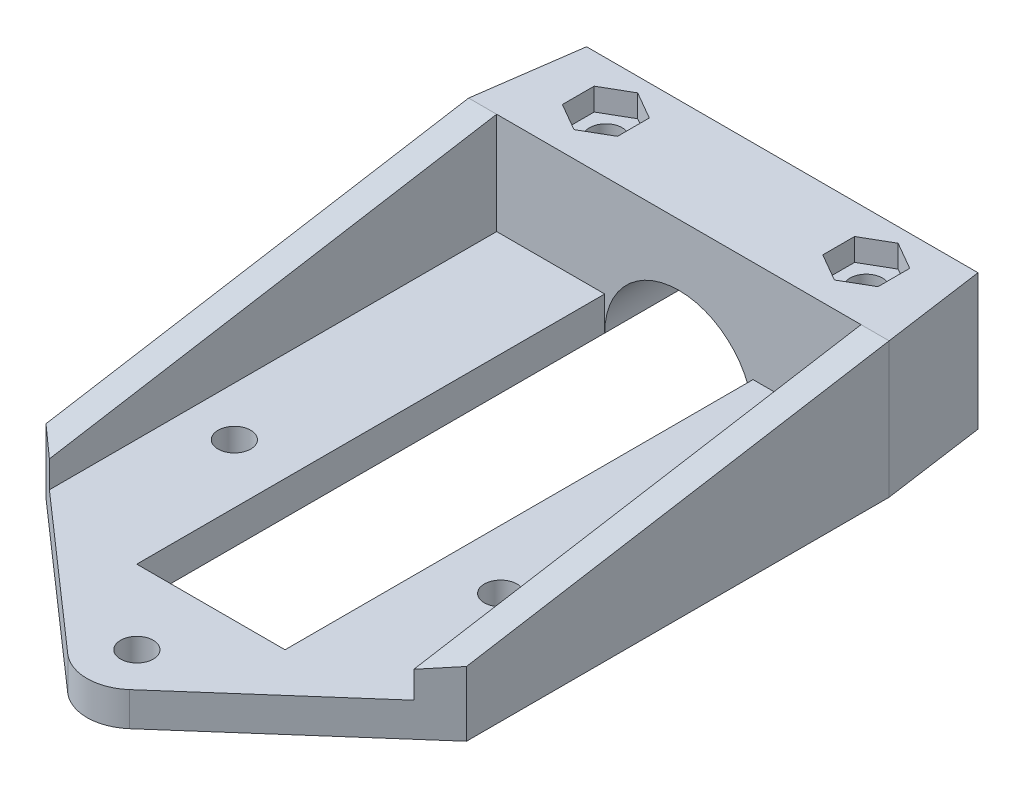
SolidWorks part; units mm, degrees
ref_plane "Front Plane" through (0, 0, 0) normal (0, 0, 1) x (1, 0, 0)
ref_plane "Top Plane" through (0, 0, 0) normal (0, 1, 0) x (1, 0, 0)
ref_plane "Right Plane" through (0, 0, 0) normal (1, 0, 0) x (0, 0, -1)
sketch "Sketch6" plane through (0, 0, 0) normal (0, 1, 0) x (1, 0, 0)
  line L0 (-16.8369, 5.7834) -> (13.1631, 5.7834)
  line L1 (13.1631, 5.7834) -> (20.6631, -47.5819)
  line L2 (20.6631, -47.5819) -> (-24.3369, -47.5819)
  line L3 (-24.3369, -47.5819) -> (-16.8369, 5.7834)
  circle A0 centre (13.1631, -5.2166) radius 1.78
  circle A1 centre (-16.8369, -5.2166) radius 1.78
  circle A2 centre (-26.4869, -43.0491) radius 1.78
  circle A3 centre (22.8131, -43.0491) radius 1.78
  dimension "D3" = 98
  dimension "D4" = 3.56
  dimension "D5" = 3.56
  dimension "D2" = 45
  dimension "D6" = 30
  dimension "D7" = 11
  dimension "D8" = 11
  dimension "D9" = 98
  dimension "D10" = 82
  dimension "D11" = 82
  dimension "D12" = 30
extrude "Boss-Extrude3" add sketch "Sketch6" along normal blind 14.5 contours L3 L0 L1 L2
sketch "Sketch8" plane through (0, 0, 47.5819) normal (0, 0, 1) x (1, 0, 0)
  line L0 (20.6631, 0) -> (-24.3369, 0) construction
  circle A0 centre (-1.8369, 0) radius 7.935
  dimension "D1" = 15.87
extrude "Cut-Extrude3" cut sketch "Sketch8" against normal blind 88
sketch "Sketch18" plane through (0, 14.5, 0) normal (0, 1, 0) x (1, 0, 0)
  line L0 (20.6631, -47.5819) -> (-24.3369, -47.5819) construction
  line L1 (-24.3369, -47.5819) -> (-16.8369, 5.7834) construction
  line L2 (13.1631, 5.7834) -> (20.6631, -47.5819) construction
  line L10 (-15.7718, -44.8683) -> (-12.8218, -43.1651)
  line L11 (-12.8218, -43.1651) -> (-12.8218, -39.7587)
  line L12 (-12.8218, -39.7587) -> (-15.7718, -38.0556)
  line L13 (-15.7718, -38.0556) -> (-18.7218, -39.7587)
  line L14 (-18.7218, -39.7587) -> (-18.7218, -43.1651)
  line L15 (-18.7218, -43.1651) -> (-15.7718, -44.8683)
  line L16 (12.098, -44.8683) -> (15.048, -43.1651)
  line L17 (15.048, -43.1651) -> (15.048, -39.7587)
  line L18 (15.048, -39.7587) -> (12.098, -38.0556)
  line L19 (12.098, -38.0556) -> (9.148, -39.7587)
  line L20 (9.148, -39.7587) -> (9.148, -43.1651)
  line L21 (9.148, -43.1651) -> (12.098, -44.8683)
  line L22 (11.3893, -26.016) -> (14.3893, -24.284)
  line L23 (14.3893, -24.284) -> (14.3893, -20.8199)
  line L24 (14.3893, -20.8199) -> (11.3893, -19.0878)
  line L25 (11.3893, -19.0878) -> (8.3893, -20.8199)
  line L26 (8.3893, -20.8199) -> (8.3893, -24.284)
  line L27 (8.3893, -24.284) -> (11.3893, -26.016)
  line L28 (-15.0632, -26.016) -> (-12.0632, -24.284)
  line L29 (-12.0632, -24.284) -> (-12.0632, -20.8199)
  line L30 (-12.0632, -20.8199) -> (-15.0632, -19.0878)
  line L31 (-15.0632, -19.0878) -> (-18.0632, -20.8199)
  line L32 (-18.0632, -20.8199) -> (-18.0632, -24.284)
  line L33 (-18.0632, -24.284) -> (-15.0632, -26.016)
  circle A0 centre (-15.0632, -22.5519) radius 3 construction
  circle A1 centre (-15.7718, -41.4619) radius 2.95 construction
  circle A2 centre (12.098, -41.4619) radius 2.95 construction
  circle A3 centre (11.3893, -22.5519) radius 3 construction
  point P0 (-15.7718, -41.4619)
  point P1 (-15.0632, -22.5519)
  point P2 (12.098, -41.4619)
  point P3 (11.3893, -22.5519)
  dimension "D1" = 6.12
  dimension "D2" = 7.63
  dimension "D3" = 25.03
  dimension "D4" = 5.7
  dimension "D5" = 6.12
  dimension "D6" = 7.63
  dimension "D7" = 25.03
  dimension "D8" = 5.7
  dimension "D9" = 6
  dimension "D10" = 5.9
  dimension "D11" = 5.9
  dimension "D12" = 6
sketch "Sketch19" plane through (0, 0, 0) normal (0, -1, 0) x (1, 0, 0)
  line L1 (-20.0152, 40.7177) -> (-17.249, 37.4149)
  line L2 (-17.249, 37.4149) -> (-13.0056, 38.1592)
  line L3 (-13.0056, 38.1592) -> (-11.5284, 42.2062)
  line L4 (-11.5284, 42.2062) -> (-14.2947, 45.5089)
  line L5 (-14.2947, 45.5089) -> (-18.5381, 44.7647)
  line L6 (-18.5381, 44.7647) -> (-20.0152, 40.7177)
  line L7 (-16.9187, 22.0232) -> (-15.5331, 20.6806)
  line L8 (-15.5331, 20.6806) -> (-13.6775, 21.2093)
  line L9 (-13.6775, 21.2093) -> (-13.2076, 23.0806)
  line L10 (-13.2076, 23.0806) -> (-14.5932, 24.4232)
  line L11 (-14.5932, 24.4232) -> (-16.4488, 23.8945)
  line L12 (-16.4488, 23.8945) -> (-16.9187, 22.0232)
  line L13 (16.8606, 20.993) -> (15.475, 26.5108)
  line L14 (15.475, 26.5108) -> (10.0037, 28.0696)
  line L15 (10.0037, 28.0696) -> (5.918, 24.1108)
  line L16 (5.918, 24.1108) -> (7.3037, 18.5931)
  line L17 (7.3037, 18.5931) -> (12.775, 17.0342)
  line L18 (12.775, 17.0342) -> (16.8606, 20.993)
  line L19 (20.0445, 40.0682) -> (17.2783, 47.6469)
  line L20 (17.2783, 47.6469) -> (9.3318, 49.0407)
  line L21 (9.3318, 49.0407) -> (4.1515, 42.8557)
  line L22 (4.1515, 42.8557) -> (6.9177, 35.2769)
  line L23 (6.9177, 35.2769) -> (14.8642, 33.8832)
  line L24 (14.8642, 33.8832) -> (20.0445, 40.0682)
  circle A0 centre (-15.7718, 41.4619) radius 3.731 construction
  circle A1 centre (-15.0632, 22.5519) radius 1.6709 construction
  circle A2 centre (11.3893, 22.5519) radius 4.9269 construction
  circle A3 centre (12.098, 41.4619) radius 6.9869 construction
  point P0 (-15.7718, 41.4619)
  point P1 (-15.0632, 22.5519)
  point P3 (11.3893, 22.5519)
  point P5 (12.098, 41.4619)
extrude "Cut-Extrude9" cut sketch "Sketch18" against normal blind 2.4
hole_wizard "#39 (0.13779528) Diameter Hole1" positions "3DSketch1" profile "Sketch21" hole size "#39" standard "ANSI Inch" end condition through all
sketch3d "3DSketch1"
  point P0 (-15.0632, 14.5, 22.5519)
  point P3 (11.3893, 14.5, 22.5519)
  point P6 (-15.7718, 14.5, 41.4619)
  point P9 (12.098, 14.5, 41.4619)
sketch "Sketch21" plane through (-15.0632, 14.5, 22.5519) normal (1, 0, 0) x (0, 0, 1)
  line L0 (0, 0) -> (0, 14.5)
  line L1 (0, 14.5) -> (1.75, 14.5)
  line L2 (1.75, 14.5) -> (1.75, 0)
  line L5 (1.75, 0) -> (0, 0)
  line L11 (0, -6.35) -> (0, 107.95) construction
  dimension "Thru Hole Dia." = 3.5
  dimension "Thru Hole Depth" = 14.5
sketch "Sketch22" plane through (0, 14.5, 0) normal (0, 1, 0) x (1, 0, 0)
  line L0 (-22.7813, -36.5132) -> (19.1075, -36.5132)
  line L1 (-24.3369, -47.5819) -> (-16.8369, 5.7834) construction
  line L2 (13.1631, 5.7834) -> (20.6631, -47.5819) construction
  line L3 (19.1075, -36.5132) -> (13.1631, 5.7834)
  line L4 (13.1631, 5.7834) -> (-16.8369, 5.7834)
  line L5 (-16.8369, 5.7834) -> (-22.7813, -36.5132)
extrude "Cut-Extrude10" cut sketch "Sketch22" against normal blind 22.4
sketch "Sketch23" plane through (0, 0, 47.5819) normal (0, 0, 1) x (1, 0, 0)
  line L0 (-24.3369, 0) -> (-24.3369, 3.625)
  line L1 (-24.3369, 14.5) -> (-24.3369, 0) construction
  line L2 (-24.3369, 3.625) -> (-8.8955, 3.625)
  line L3 (20.6631, 0) -> (20.6631, 3.625)
  line L4 (20.6631, 14.5) -> (20.6631, 0) construction
  line L5 (20.6631, 3.625) -> (5.2217, 3.625)
  line L6 (-24.3369, 0) -> (-9.7719, 0)
  line L7 (20.6631, 0) -> (6.0981, 0) construction
  arc A0 (6.0981, 0) -> (-9.7719, 0) centre (-1.8369, 0) ccw construction
  spline S0 degree 2 poles (-9.7719, 0) (-9.7646, 1.9214) (-8.8955, 3.625) knots 0 0 0 1 1 1
  spline S1 degree 2 poles (6.0981, 0) (6.0907, 1.9214) (5.2217, 3.625) knots 0 0 0 1 1 1
  dimension "D1" = 3.625
  dimension "D2" = 3.625
sketch "Sketch24" plane through (0, 0, 0) normal (0, -1, 0) x (1, 0, 0)
  line L1 (-15.7718, 38.0556) -> (-12.8218, 39.7587)
  line L2 (-12.8218, 39.7587) -> (-12.8218, 43.1651)
  line L3 (-12.8218, 43.1651) -> (-15.7718, 44.8683)
  line L4 (-15.7718, 44.8683) -> (-18.7218, 43.1651)
  line L5 (-18.7218, 43.1651) -> (-18.7218, 39.7587)
  line L6 (-18.7218, 39.7587) -> (-15.7718, 38.0556)
  line L7 (12.098, 38.0556) -> (15.048, 39.7587)
  line L8 (15.048, 39.7587) -> (15.048, 43.1651)
  line L9 (15.048, 43.1651) -> (12.098, 44.8683)
  line L10 (12.098, 44.8683) -> (9.148, 43.1651)
  line L11 (9.148, 43.1651) -> (9.148, 39.7587)
  line L12 (9.148, 39.7587) -> (12.098, 38.0556)
  circle A0 centre (-15.7718, 41.4619) radius 2.95 construction
  circle A1 centre (12.098, 41.4619) radius 2.95 construction
  point P0 (-15.7718, 41.4619)
  point P1 (12.098, 41.4619)
  dimension "D1" = 5.9
  dimension "D2" = 5.9
extrude "Cut-Extrude11" cut sketch "Sketch24" against normal blind 2.4
sketch "Sketch27" plane through (0, 0, 0) normal (0, 1, 0) x (1, 0, 0)
  line L0 (-9.7719, -47.2249) -> (-9.7719, -47.5819)
  line L1 (-9.7719, -47.5819) -> (-9.7719, -97.6619)
  line L2 (-9.7719, -112.5819) -> (-24.3369, -112.5819)
  line L3 (-24.3369, -112.5819) -> (-24.3369, -47.5819)
  line L4 (-9.7719, -97.6619) -> (6.0981, -97.6619)
  line L5 (6.0981, -47.5819) -> (6.0981, -97.6619)
  line L6 (20.6631, -47.5819) -> (20.6631, -112.5819)
  line L7 (20.6631, -112.5819) -> (-9.7719, -112.5819)
  line L9 (-24.3369, -47.5819) -> (-9.7719, -47.5819)
  line L10 (-24.3369, -47.5819) -> (-9.7719, -47.5819)
  line L11 (6.0981, -47.5819) -> (20.6631, -47.5819)
  dimension "D1" = 65
  dimension "D2" = 14.92
  dimension "D3" = 15.87
extrude "Boss-Extrude7" add sketch "Sketch27" along normal up to vertex (3.625 mm away) contours L11 L5 L4 L1 L9 L3 L2 L7 L6 up to point (20.6631, 3.625, 47.5819)
sketch "Sketch30" plane through (0, 3.625, 0) normal (0, 1, 0) x (1, 0, 0)
  line L0 (20.6631, -112.5819) -> (-24.3369, -112.5819) construction
  line L2 (20.6631, -47.5819) -> (20.6631, -112.5819) construction
  line L3 (-16.0869, -80.9002) -> (-1.8369, -105.5819)
  line L4 (-1.8369, -105.5819) -> (12.4131, -80.9002)
  line L5 (12.4131, -80.9002) -> (-16.0869, -80.9002)
  line L6 (6.0981, -47.5819) -> (6.0981, -97.6619) construction
  line L7 (-9.7719, -47.5819) -> (-9.7719, -97.6619) construction
  point P0 (-16.0869, -80.9002)
  point P1 (12.4131, -80.9002)
  point P2 (-1.8369, -105.5819)
  dimension "D2" = 28.5
  dimension "D3" = 28.5
  dimension "D4" = 60
  dimension "D5" = 60
  dimension "D6" = 22.5
  dimension "D7" = 60
  dimension "D8" = 6.315
  dimension "D9" = 6.315
  dimension "D10" = 7
  dimension "D11" = 28.5
hole_wizard "#39 (0.13779528) Diameter Hole2" positions "3DSketch2" profile "Sketch31" hole size "#39" standard "ANSI Inch" end condition through all
sketch3d "3DSketch2"
  point P0 (-16.0869, 3.625, 80.9002)
  point P3 (-1.8369, 3.625, 105.5819)
  point P6 (12.4131, 3.625, 80.9002)
sketch "Sketch31" plane through (-16.0869, 3.625, 80.9002) normal (1, 0, 0) x (0, 0, 1)
  line L0 (0, 0) -> (0, 3.625)
  line L1 (0, 3.625) -> (1.75, 3.625)
  line L2 (1.75, 3.625) -> (1.75, 0)
  line L5 (1.75, 0) -> (0, 0)
  line L11 (0, -6.35) -> (0, 107.95) construction
  dimension "Thru Hole Dia." = 3.5
  dimension "Thru Hole Depth" = 3.625
sketch "Sketch39" plane through (20.6631, 0, 0) normal (1, 0, 0) x (0, 0, -1)
  line L0 (-47.5819, 14.5) -> (-112.5819, 3.625)
  line L1 (-112.5819, 3.625) -> (-47.5819, 3.625)
  line L2 (-47.5819, 3.625) -> (-47.5819, 14.5)
extrude "Boss-Extrude10" add sketch "Sketch39" against normal blind 3
sketch "Sketch40" plane through (-24.3369, 0, 0) normal (-1, 0, 0) x (0, 0, 1)
  line L0 (47.5819, 14.5) -> (112.5819, 3.625)
  line L1 (112.5819, 3.625) -> (47.5819, 3.625)
  line L2 (47.5819, 3.625) -> (47.5819, 14.5)
extrude "Boss-Extrude11" add sketch "Sketch40" against normal blind 3
sketch "Sketch42" plane through (0, 3.625, 0) normal (0, 1, 0) x (1, 0, 0)
  line L0 (-1.8369, -112.5819) -> (20.6631, -92.8102)
  line L1 (17.6631, -112.5819) -> (-21.3369, -112.5819) construction
  line L2 (20.6631, -47.5819) -> (20.6631, -112.5819) construction
  line L3 (20.6631, -92.8102) -> (20.6631, -112.5819)
  line L4 (20.6631, -112.5819) -> (-1.8369, -112.5819)
  line L5 (-1.8369, -112.5819) -> (-24.3369, -92.8102)
  line L6 (-24.3369, -112.5819) -> (-24.3369, -47.5819) construction
  line L7 (-24.3369, -92.8102) -> (-24.3369, -112.5819)
  line L8 (-24.3369, -112.5819) -> (-1.8369, -112.5819)
  line L9 (-24.3369, -92.8102) -> (-1.8369, -112.5819)
  line L10 (-24.3369, -112.5819) -> (-24.3369, -92.8102)
  line L11 (-1.8369, -112.5819) -> (-24.3369, -112.5819)
  line L12 (-24.3369, -92.8102) -> (-24.3369, -112.5819)
  line L13 (-24.3369, -92.8102) -> (-1.8369, -112.5819)
sketch "Sketch43" plane through (0, 0, 0) normal (0, -1, 0) x (1, 0, 0)
  line L0 (-24.3369, 112.5819) -> (-24.3369, 92.8102)
  line L1 (-24.3369, 92.8102) -> (-1.8369, 112.5819)
  line L2 (-1.8369, 112.5819) -> (-24.3369, 112.5819)
  line L3 (-1.8369, 112.5819) -> (20.6631, 112.5819)
  line L4 (20.6631, 112.5819) -> (20.6631, 92.8102)
  line L5 (20.6631, 92.8102) -> (-1.8369, 112.5819)
  line M19 (20.6631, 112.5819) -> (-24.3369, 112.5819)
  line M20 (-24.3369, 112.5819) -> (-24.3369, 47.5819)
extrude "Cut-Extrude14" cut sketch "Sketch43" against normal blind 13 contours L1 M20 M19
sketch "Sketch44" plane through (0, 0, 0) normal (0, -1, 0) x (1, 0, 0)
  line L0 (20.6631, 92.8102) -> (20.6631, 112.5819)
  line L1 (20.6631, 112.5819) -> (-1.8369, 112.5819)
  line L2 (-1.8369, 112.5819) -> (20.6631, 92.8102)
extrude "Cut-Extrude15" cut sketch "Sketch44" against normal blind 13
fillet "Fillet1" radius 5 1 edges at (-1.8369, 1.8125, 112.5819)
